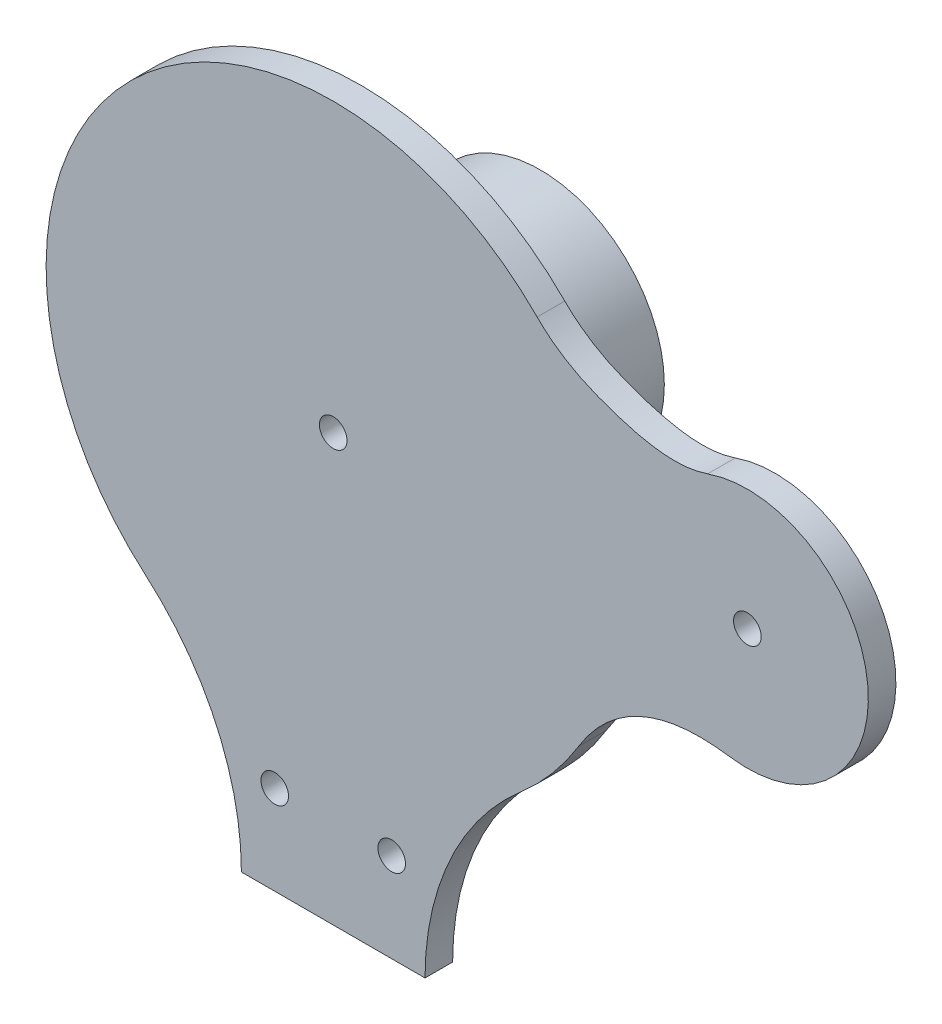
SolidWorks part; units mm, degrees
ref_plane "Front Plane" through (0, 0, 0) normal (0, 0, 1) x (1, 0, 0)
ref_plane "Top Plane" through (0, 0, 0) normal (0, 1, 0) x (1, 0, 0)
ref_plane "Right Plane" through (0, 0, 0) normal (1, 0, 0) x (0, 0, -1)
sketch "Sketch1" plane through (0, 0, 0) normal (0, 0, 1) x (1, 0, 0)
  line L0 (-16.891, -131.2827) -> (16.891, -131.2827)
  arc A4 (-16.891, -131.2827) -> (-27.4428, -100.2871) centre (-67.691, -131.2827) ccw
  arc A5 (-27.4428, -100.2871) -> (-34.5065, -92.8193) centre (-67.691, -131.2827) ccw
  arc A6 (27.4428, -100.2871) -> (16.891, -131.2827) centre (67.691, -131.2827) ccw
  arc A7 (34.5065, -92.8193) -> (27.4428, -100.2871) centre (67.691, -131.2827) ccw
  arc A8 (34.5065, -92.8193) -> (-34.5065, -92.8193) centre (0, -52.8237) ccw
  circle A9 centre (-10.7564, -114.872) radius 2.54
  circle A10 centre (10.7564, -114.872) radius 2.54
extrude "Boss-Extrude1" add sketch "Sketch1" along normal blind 5.08
sketch "Sketch2" plane through (0, 0, 0) normal (0, 0, -1) x (-1, 0, 0)
  circle A0 centre (0, -52.8237) radius 22.8255
extrude "Boss-Extrude2" add sketch "Sketch2" along normal blind 33.02
sketch "Sketch3" plane through (0, 0, -33.02) normal (0, 0, -1) x (-1, 0, 0)
  circle A0 centre (0, -52.8237) radius 2.54
  dimension "D1" = 5.08
extrude "Cut-Extrude1" cut sketch "Sketch3" against normal through all
sketch "Sketch4" plane through (0, 0, 5.08) normal (0, 0, 1) x (1, 0, 0)
  arc A0 (34.5065, -92.8193) -> (-34.5065, -92.8193) centre (0, -52.8237) ccw construction
  arc A1 (72.9914, -67.9939) -> (68.9002, -24.9499) centre (76.2, -45.9725) ccw construction
  arc A2 (45.1618, -80.2237) -> (37.5246, -15.6451) centre (0, -52.8237) ccw
  arc A3 (72.9914, -67.9939) -> (68.9002, -24.9499) centre (76.2, -45.9725) ccw
  spline S0 degree 3 poles (2241.1123, -3403.3066) (225.1714, -888.0972) (-373.5636, 821.9772) (856.2689, -1026.8223) (2675.8786, -3104.0539) knots -10.536089 -10.536089 -10.536089 -10.536089 0.395495 14.087862 14.087862 14.087862 14.087862 only from (45.1618, -80.2237) to (72.9914, -67.9939) construction
  spline S1 degree 3 poles (624.1982, 3939.7978) (0.1149, 123.7987) (-39.2199, -106.0474) (246.8712, 8.3138) (-1145.0951, 3780.6403) knots -6.214706 -6.214706 -6.214706 -6.214706 0.47993 6.272298 6.272298 6.272298 6.272298 only from (37.5246, -15.6451) to (68.9002, -24.9499) construction
  spline S2 degree 3 poles (45.1618, -80.2237) (47.5743, -76.2473) (55.0334, -68.6407) (65.5082, -66.9035) (72.9914, -67.9939) knots 0 0 0 0 0.395495 1 1 1 1
  spline S3 degree 3 poles (37.5246, -15.6451) (41.5693, -19.7274) (51.3897, -24.4152) (63.2972, -26.8954) (68.9002, -24.9499) knots 0 0 0 0 0.47993 1 1 1 1
extrude "Boss-Extrude3" add sketch "Sketch4" against normal up to surface (5.08 mm away) up to face at (22.8255, -52.8237, 0)
sketch "Sketch5" plane through (0, 0, 5.08) normal (0, 0, 1) x (1, 0, 0)
  circle A0 centre (76.2, -45.9725) radius 2.54
extrude "Cut-Extrude2" cut sketch "Sketch5" against normal through all
